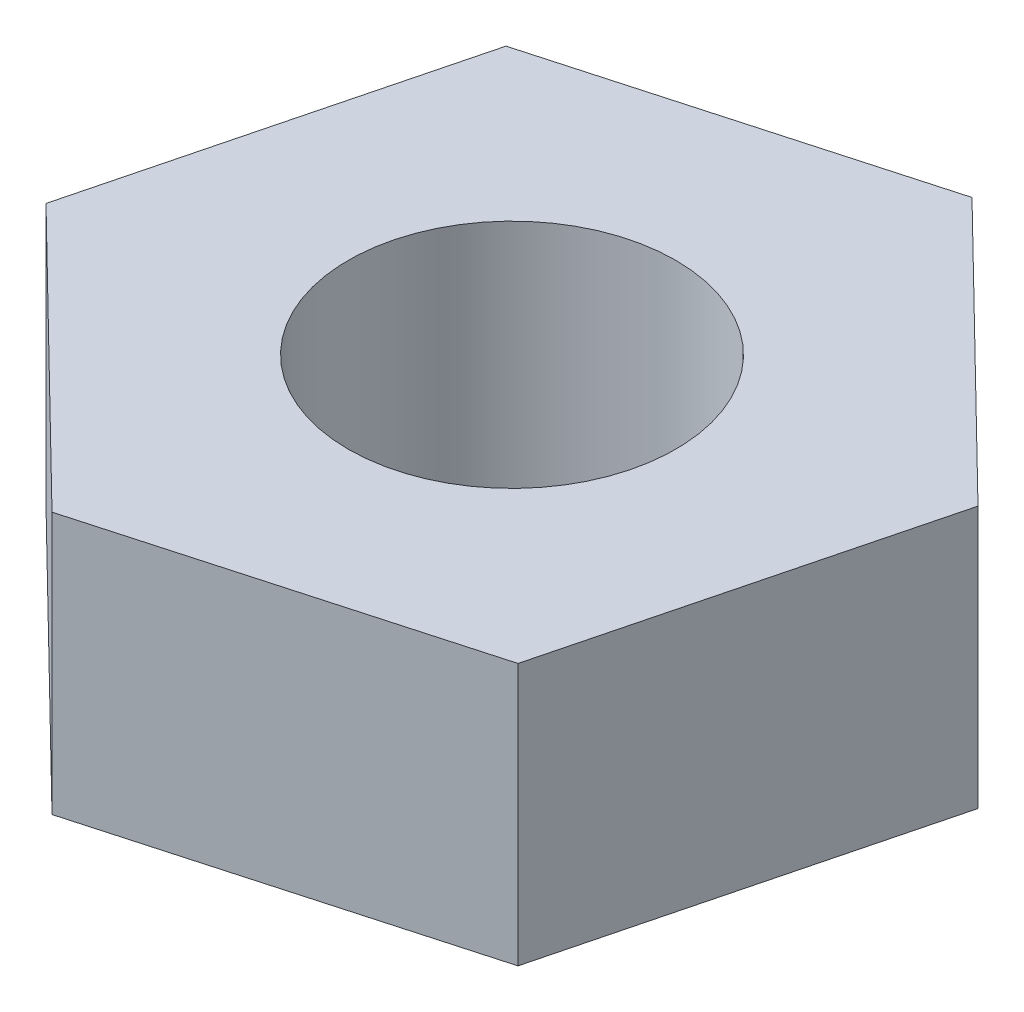
SolidWorks part; units mm, degrees
ref_plane "前视基准面" through (0, 0, 0) normal (0, 0, 1) x (1, 0, 0)
ref_plane "上视基准面" through (0, 0, 0) normal (0, 1, 0) x (1, 0, 0)
ref_plane "右视基准面" through (0, 0, 0) normal (1, 0, 0) x (0, 0, -1)
sketch "草图1" plane through (0, 0, 0) normal (0, 1, 0) x (1, 0, 0)
  line L1 (1.6512, -1.6145) -> (2.2239, 0.6227)
  line L2 (2.2239, 0.6227) -> (0.5726, 2.2373)
  line L3 (0.5726, 2.2373) -> (-1.6512, 1.6145)
  line L4 (-1.6512, 1.6145) -> (-2.2239, -0.6227)
  line L5 (-2.2239, -0.6227) -> (-0.5726, -2.2373)
  line L6 (-0.5726, -2.2373) -> (1.6512, -1.6145)
  circle A0 centre (0, 0) radius 1
  circle A1 centre (0, 0) radius 2 construction
  dimension "D1" = 2
  dimension "D2" = 4
extrude "凸台-拉伸1" add sketch "草图1" along normal blind 1.6
